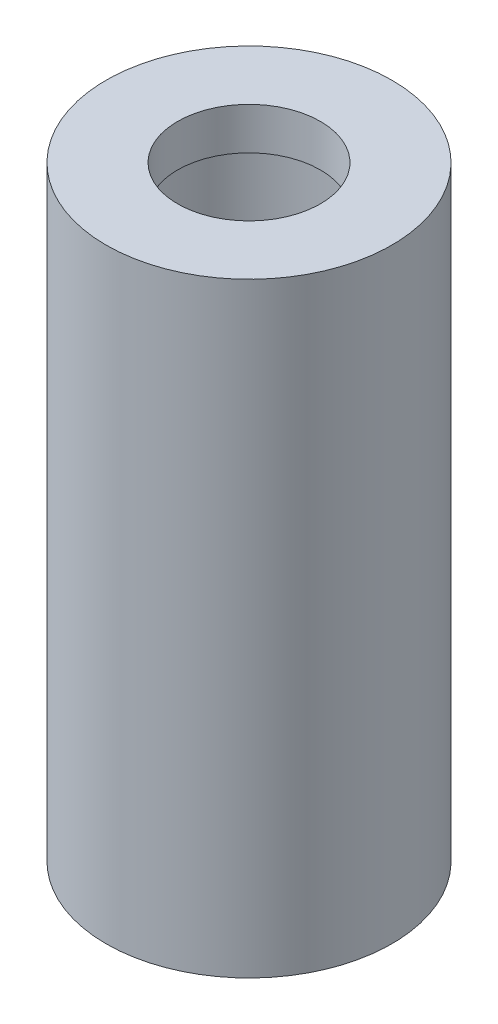
SolidWorks part; units mm, degrees
material "1060 Alloy"
ref_plane "Front Plane" through (0, 0, 0) normal (0, 0, 1) x (1, 0, 0)
ref_plane "Top Plane" through (0, 0, 0) normal (0, 1, 0) x (1, 0, 0)
ref_plane "Right Plane" through (0, 0, 0) normal (1, 0, 0) x (0, 0, -1)
sketch "Sketch2" plane through (0, 0, 0) normal (0, 0, 1) x (1, 0, 0)
  line L0 (0, 0) -> (0, 7.3) construction
  line L1 (3.175, 0) -> (4.318, 0)
  line L2 (2.159, 17.018) -> (2.159, 18.288)
  line L3 (2.159, 18.288) -> (4.318, 18.288)
  line L4 (4.318, 0) -> (4.318, 18.288)
  line L7 (2.159, 17.018) -> (2.921, 17.018)
  line L8 (3.175, 0) -> (3.175, 12.7)
  line L9 (3.175, 13.97) -> (0, 13.97) construction
  line L10 (3.175, 12.7) -> (0, 12.7) construction
  line L11 (2.921, 17.018) -> (2.921, 12.7)
  line L12 (2.921, 12.7) -> (3.175, 12.7)
  dimension "D1" = 4.318
  dimension "D2" = 8.636
  dimension "D3" = 6.35
  dimension "D4" = 12.7
  dimension "D5" = 1.27
  dimension "D6" = 1.27
  dimension "D7" = 3.048
  dimension "D8" = 0.254
revolve "Revolve1" add sketch "Sketch2" angle 360 about L0
sketch "Sketch3" plane through (0, 0, 0) normal (0, 0, 1) x (1, 0, 0)
  line L0 (4.318, 18.288) -> (-4.318, 18.288) construction
  circle A0 centre (0, 8.128) radius 2.032
  dimension "D1" = 4.064
  dimension "D2" = 10.16
extrude "Cut-Extrude1" cut sketch "Sketch3" against normal through all
